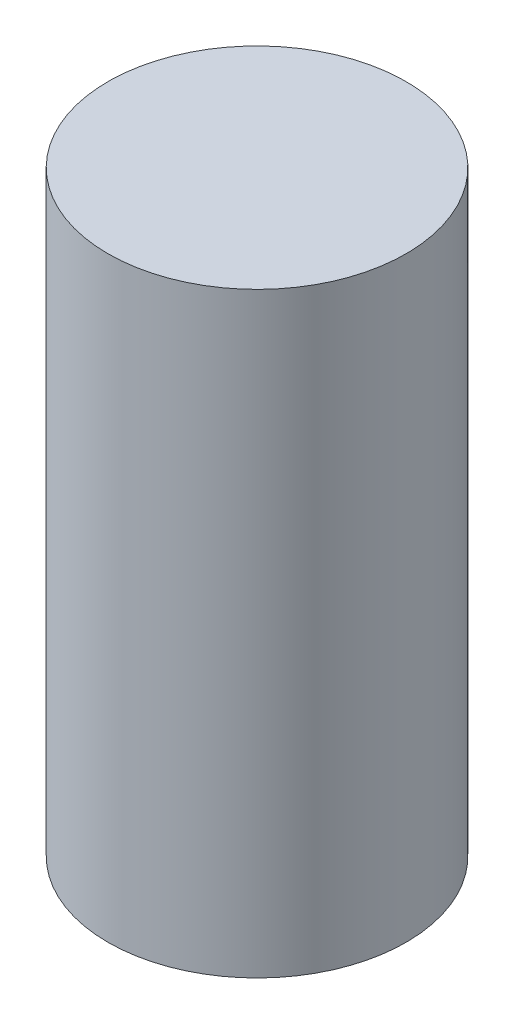
SolidWorks part; units mm, degrees
ref_plane "Front Plane" through (0, 0, 0) normal (0, 0, 1) x (1, 0, 0)
ref_plane "Top Plane" through (0, 0, 0) normal (0, 1, 0) x (1, 0, 0)
ref_plane "Right Plane" through (0, 0, 0) normal (1, 0, 0) x (0, 0, -1)
sketch "Sketch1" plane through (0, 0, 0) normal (0, 1, 0) x (1, 0, 0)
  circle A0 centre (109.8173, -139.2905) radius 5
  dimension "D1" = 10
extrude "Boss-Extrude1" add sketch "Sketch1" along normal blind 20
ref_plane "Plane1" through (114.8173, 0, 0) normal (1, 0, 0) x (0, 0, -1)
